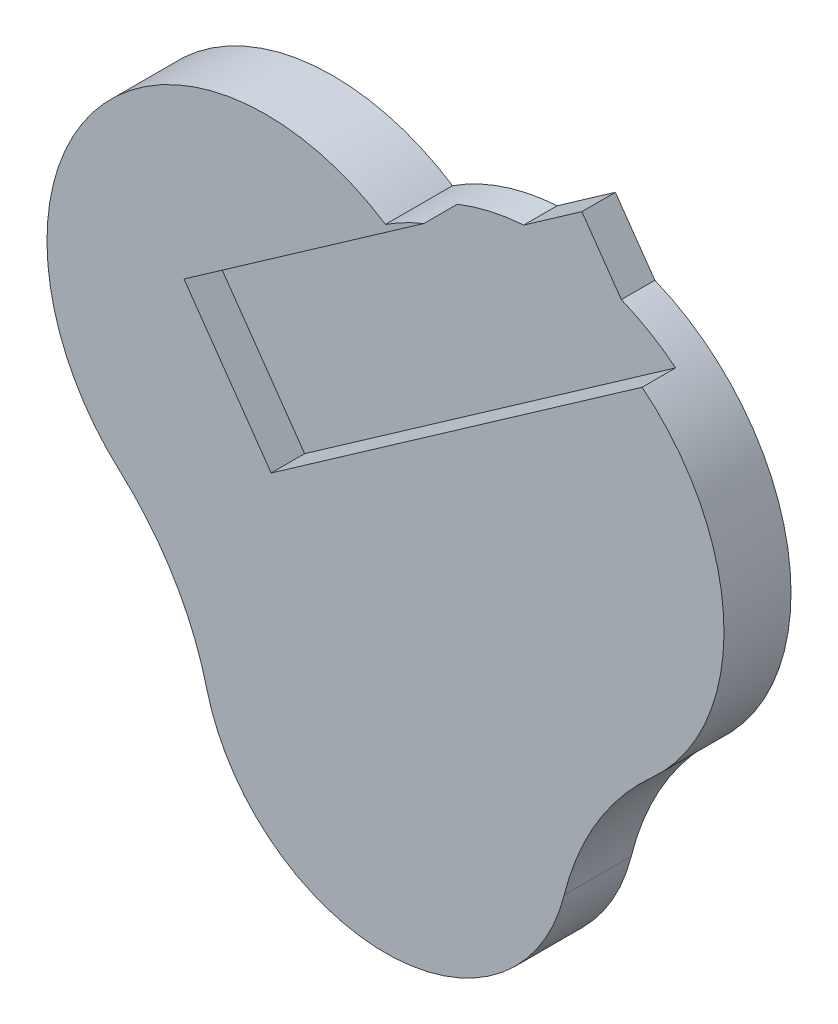
SolidWorks part; units mm, degrees
ref_plane "Front Plane" through (0, 0, 0) normal (0, 0, 1) x (1, 0, 0)
ref_plane "Top Plane" through (0, 0, 0) normal (0, 1, 0) x (1, 0, 0)
ref_plane "Right Plane" through (0, 0, 0) normal (1, 0, 0) x (0, 0, -1)
sketch "Sketch2" plane through (0, 0, 0) normal (0, 0, 1) x (1, 0, 0)
  line L0 (0, 0) -> (0, 159.7945) construction
  line L1 (0, 159.7945) -> (192.4598, 159.7945) construction
  line L2 (0, 159.7945) -> (192.4598, 294.5563) construction
  line L3 (192.4598, 294.5563) -> (192.4598, 159.7945) construction
  line L5 (-61.4343, 82.5337) -> (240.9633, 82.5337) construction
  line L6 (21.7922, 175.0536) -> (157.7368, 175.0536) construction
  line L7 (89.7645, 25.2954) -> (89.7645, 175.0536) construction
  line L8 (-11.8355, 0) -> (191.3645, 0) construction
  line L9 (0, 159.7945) -> (24.767, 124.4236)
  line L10 (24.767, 124.4236) -> (235.6533, 272.0877)
  line L11 (0, 159.7945) -> (-24.767, 195.1655)
  line L12 (-24.767, 195.1655) -> (111.5321, 290.6032)
  arc A0 (-11.8355, 0) -> (191.3645, 0) centre (89.7645, 25.2954) ccw
  arc A1 (89.7645, 279.2954) -> (-61.4343, 82.5337) centre (21.7922, 175.0536) ccw
  arc A2 (240.9633, 82.5337) -> (235.6533, 272.0877) centre (157.7368, 175.0536) ccw
  arc A3 (-11.8355, 0) -> (-61.4343, 82.5337) centre (-171.4181, -39.7314) ccw
  arc A4 (240.9633, 82.5337) -> (191.3645, 0) centre (350.9472, -39.7314) ccw
  arc A5 (111.5321, 290.6032) -> (89.7645, 279.2954) centre (157.7368, 175.0536) ccw
  arc A6 (111.5321, 290.6032) -> (235.6533, 272.0877) centre (157.7368, 175.0536) cw construction
  dimension "D5" = 86.36
  dimension "D6" = 135.9446
  dimension "D7" = 203.2
  dimension "D8" = 254
  dimension "D9" = 104.7016
  dimension "D4" = 124.4451
  dimension "D2" = 234.95
  dimension "D3" = 35
  dimension "D10" = 82.5337
  dimension "D11" = 159.7945
extrude "Boss-Extrude1" add sketch "Sketch2" along normal blind 38.1 contours A1 A3 A0 A4 A2 L10 L9 L11 L12 A5
sketch "Sketch3" plane through (0, 0, 0) normal (0, 0, -1) x (-1, 0, 0)
  line L0 (24.767, 195.1655) -> (-24.767, 124.4236)
  line L1 (-24.767, 124.4236) -> (-235.6533, 272.0877)
  line L2 (-111.5321, 290.6032) -> (24.767, 195.1655)
  arc A0 (-111.5321, 290.6032) -> (-235.6533, 272.0877) centre (-157.7368, 175.0536) ccw
  arc A1 (-235.6533, 272.0877) -> (-240.9633, 82.5337) centre (-157.7368, 175.0536) ccw construction
extrude "Boss-Extrude2" add sketch "Sketch3" against normal blind 19.05 separate body
sketch "Sketch4" plane through (0, 0, 0) normal (0, 0, -1) x (-1, 0, 0)
  line L0 (-111.5321, 290.6032) -> (-119.9092, 278.6395)
  line L1 (-235.6533, 272.0877) -> (-24.767, 124.4236) construction
  line L2 (-152.6891, 231.8249) -> (-215.1085, 275.5315)
  line L3 (-215.1085, 275.5315) -> (-182.3286, 322.346)
  line L4 (-182.3286, 322.346) -> (-119.9092, 278.6395)
  line L5 (-152.6891, 231.8249) -> (-161.0662, 219.8612)
  line L6 (-152.6891, 231.8249) -> (-119.9092, 278.6395)
  arc M2 (-111.5321, 290.6032) -> (-235.6533, 272.0877) centre (-157.7368, 175.0536) ccw
  dimension "D1" = 57.15
  dimension "D2" = 76.2
extrude "Boss-Extrude3" add sketch "Sketch4" along direction (0, 0, 1) on the side against the normal up to surface (19.05 mm away) contours L4 L3 L2 M2
